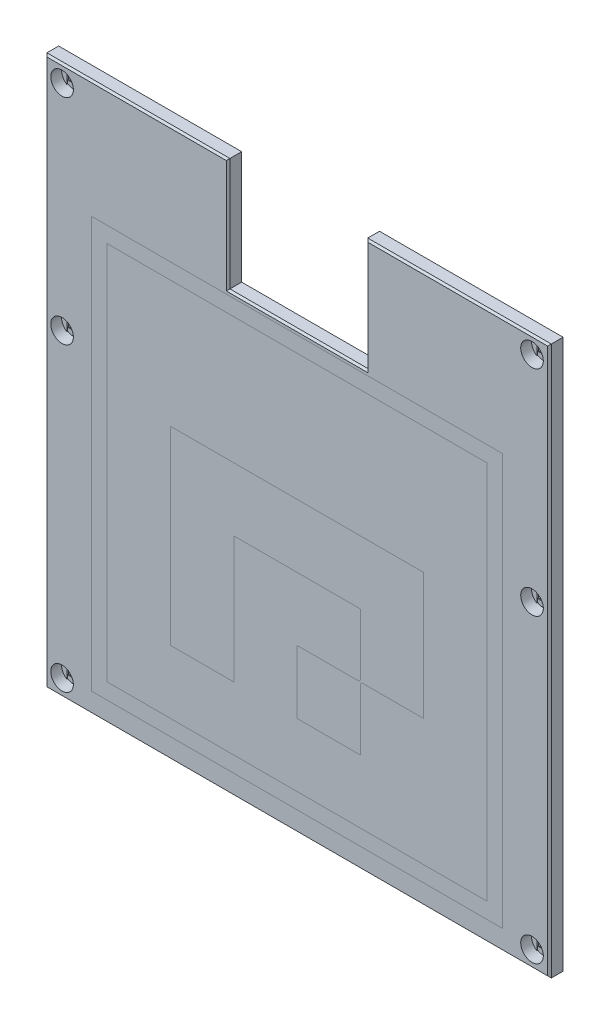
SolidWorks part; units mm, degrees
ref_plane "Front Plane" through (0, 0, 0) normal (0, 0, 1) x (1, 0, 0)
ref_plane "Top Plane" through (0, 0, 0) normal (0, 1, 0) x (1, 0, 0)
ref_plane "Right Plane" through (0, 0, 0) normal (1, 0, 0) x (0, 0, -1)
sketch "Sketch1" plane through (0, 0, 0) normal (0, 0, 1) x (1, 0, 0)
  line L0 (48, -68) -> (-48, -68) construction
  line L1 (56, -32.5) -> (56, -60) construction
  line L2 (56, 46) -> (56, -24.5) construction
  line L3 (-56, -24.5) -> (-56, 46) construction
  line L5 (-15, 54.4) -> (-15, 29) construction
  line L6 (-15, 29) -> (15, 29) construction
  line L8 (48, 54) -> (15, 54) construction
  line L9 (48, -68) -> (-48, -68) construction
  line L10 (56, -32.5) -> (56, -60) construction
  line L11 (56, 46) -> (56, -24.5) construction
  line L12 (-56, -24.5) -> (-56, 46) construction
  line L14 (-15, 54.4) -> (-15, 29) construction
  line L15 (-15, 29) -> (15, 29) construction
  line L16 (15, 29) -> (15, 54) construction
  line L17 (48, 54) -> (15, 54) construction
  line L18 (-15.25, 53.75) -> (-15.25, 28.75)
  line L19 (-55.75, 53.75) -> (-15.25, 53.75)
  line L20 (-55.75, 53.75) -> (-55.75, -67.75)
  line L21 (-55.75, -67.75) -> (55.875, -67.75)
  line L22 (55.875, 53.75) -> (55.875, -67.75)
  line L23 (-15.25, 28.75) -> (15.25, 28.75)
  line L24 (15.25, 28.75) -> (15.25, 53.75)
  line L25 (15.25, 53.75) -> (55.875, 53.75)
  circle A0 centre (-52, -64) radius 2.1 construction
  circle A3 centre (52, 50) radius 2.1 construction
  circle A4 centre (-52, 50) radius 2.1 construction
  circle A5 centre (-52, -64) radius 2.1 construction
  circle A6 centre (-52, 2.6) radius 2.15 construction
  circle A7 centre (52, 2.6) radius 2.15 construction
  circle A8 centre (52, 50) radius 2.1 construction
  circle A9 centre (-52, 50) radius 2.1 construction
  circle A10 centre (-52, 50) radius 1.35
  circle A11 centre (-52, 2.6) radius 1.35
  circle A12 centre (-52, -64) radius 1.35
  circle A13 centre (52, 50) radius 1.35
  circle A14 centre (52, 2.6) radius 1.35
  circle A15 centre (52, -64) radius 1.35
  circle A16 centre (-52, 2.6) radius 2.15 construction
  circle A17 centre (52, 2.6) radius 2.15 construction
  dimension "D5" = 2.7
  dimension "D1" = 0.25
  dimension "D2" = 0.25
  dimension "D3" = 0.25
  dimension "D4" = 0.25
  dimension "D6" = 0.25
  dimension "D7" = 0.25
  dimension "D8" = 0.25
extrude "Boss-Extrude1" add sketch "Sketch1" along normal blind 3
sketch "Sketch2" plane through (0, 0, 3) normal (0, 0, 1) x (1, 0, 0)
  line L5 (15.25, 28.75) -> (-15.25, 28.75) construction
  line L8 (-45.5, -63.25) -> (45.5, -63.25)
  line L9 (-45.5, -63.25) -> (-45.5, 27.75)
  line L10 (-45.5, 27.75) -> (45.5, 27.75)
  line L11 (45.5, -63.25) -> (45.5, 27.75)
  line L31 (-42, 24.25) -> (-28, 24.25)
  line L32 (-42, 24.25) -> (-42, 10.25)
  line L33 (-42, 10.25) -> (-28, 10.25)
  line L34 (-28, 24.25) -> (-28, 10.25)
  line L35 (-28, 24.25) -> (-14, 24.25)
  line L36 (-28, 24.25) -> (-28, 10.25)
  line L37 (-28, 10.25) -> (-14, 10.25)
  line L38 (-14, 24.25) -> (-14, 10.25)
  line L39 (-14, 24.25) -> (0, 24.25)
  line L40 (-14, 24.25) -> (-14, 10.25)
  line L41 (-14, 10.25) -> (0, 10.25)
  line L42 (0, 24.25) -> (0, 10.25)
  line L43 (0, 24.25) -> (14, 24.25)
  line L44 (0, 24.25) -> (0, 10.25)
  line L45 (0, 10.25) -> (14, 10.25)
  line L46 (14, 24.25) -> (14, 10.25)
  line L47 (14, 24.25) -> (28, 24.25)
  line L48 (14, 24.25) -> (14, 10.25)
  line L49 (14, 10.25) -> (28, 10.25)
  line L50 (28, 24.25) -> (28, 10.25)
  line L51 (28, 24.25) -> (42, 24.25)
  line L52 (28, 24.25) -> (28, 10.25)
  line L53 (28, 10.25) -> (42, 10.25)
  line L54 (42, 24.25) -> (42, 10.25)
  line L55 (-42, 10.25) -> (-28, 10.25)
  line L56 (-42, 10.25) -> (-42, -3.75)
  line L57 (-42, -3.75) -> (-28, -3.75)
  line L58 (-28, 10.25) -> (-28, -3.75)
  line L59 (-28, -3.75) -> (-14, -3.75)
  line L60 (-28, -3.75) -> (-28, 10.25)
  line L61 (-28, 10.25) -> (-14, 10.25)
  line L62 (-14, -3.75) -> (-14, 10.25)
  line L63 (-14, -3.75) -> (0, -3.75)
  line L64 (-14, -3.75) -> (-14, 10.25)
  line L65 (-14, 10.25) -> (0, 10.25)
  line L66 (0, -3.75) -> (0, 10.25)
  line L67 (0, -3.75) -> (14, -3.75)
  line L68 (0, -3.75) -> (0, 10.25)
  line L69 (0, 10.25) -> (14, 10.25)
  line L70 (14, -3.75) -> (14, 10.25)
  line L71 (14, -3.75) -> (28, -3.75)
  line L72 (14, -3.75) -> (14, 10.25)
  line L73 (14, 10.25) -> (28, 10.25)
  line L74 (28, -3.75) -> (28, 10.25)
  line L75 (28, -3.75) -> (42, -3.75)
  line L76 (28, -3.75) -> (28, 10.25)
  line L77 (28, 10.25) -> (42, 10.25)
  line L78 (42, -3.75) -> (42, 10.25)
  line L79 (42, -3.75) -> (28, -3.75)
  line L80 (42, -3.75) -> (42, -17.75)
  line L81 (42, -17.75) -> (28, -17.75)
  line L82 (28, -3.75) -> (28, -17.75)
  line L83 (14, -3.75) -> (28, -3.75)
  line L84 (14, -3.75) -> (14, -17.75)
  line L85 (14, -17.75) -> (28, -17.75)
  line L86 (28, -3.75) -> (28, -17.75)
  line L87 (0, -3.75) -> (14, -3.75)
  line L88 (0, -3.75) -> (0, -17.75)
  line L89 (0, -17.75) -> (14, -17.75)
  line L90 (14, -3.75) -> (14, -17.75)
  line L91 (-14, -3.75) -> (0, -3.75)
  line L92 (-14, -3.75) -> (-14, -17.75)
  line L93 (-14, -17.75) -> (0, -17.75)
  line L94 (0, -3.75) -> (0, -17.75)
  line L95 (-28, -3.75) -> (-14, -3.75)
  line L96 (-28, -3.75) -> (-28, -17.75)
  line L97 (-28, -17.75) -> (-14, -17.75)
  line L98 (-14, -3.75) -> (-14, -17.75)
  line L99 (-42, -3.75) -> (-28, -3.75)
  line L100 (-42, -3.75) -> (-42, -17.75)
  line L101 (-42, -17.75) -> (-28, -17.75)
  line L102 (-28, -3.75) -> (-28, -17.75)
  line L103 (-42, -17.75) -> (-28, -17.75)
  line L104 (-42, -17.75) -> (-42, -31.75)
  line L105 (-42, -31.75) -> (-28, -31.75)
  line L106 (-28, -17.75) -> (-28, -31.75)
  line L107 (-28, -31.75) -> (-14, -31.75)
  line L108 (-28, -31.75) -> (-28, -17.75)
  line L109 (-28, -17.75) -> (-14, -17.75)
  line L110 (-14, -31.75) -> (-14, -17.75)
  line L111 (-14, -17.75) -> (0, -17.75)
  line L112 (-14, -17.75) -> (-14, -31.75)
  line L113 (-14, -31.75) -> (0, -31.75)
  line L114 (0, -17.75) -> (0, -31.75)
  line L115 (0, -31.75) -> (14, -31.75)
  line L116 (0, -31.75) -> (0, -17.75)
  line L117 (0, -17.75) -> (14, -17.75)
  line L118 (14, -31.75) -> (14, -17.75)
  line L119 (14, -31.75) -> (28, -31.75)
  line L120 (14, -31.75) -> (14, -17.75)
  line L121 (14, -17.75) -> (28, -17.75)
  line L122 (28, -31.75) -> (28, -17.75)
  line L123 (28, -31.75) -> (42, -31.75)
  line L124 (28, -31.75) -> (28, -17.75)
  line L125 (28, -17.75) -> (42, -17.75)
  line L126 (42, -31.75) -> (42, -17.75)
  line L127 (-42, -31.75) -> (-28, -31.75)
  line L128 (-42, -31.75) -> (-42, -45.75)
  line L129 (-42, -45.75) -> (-28, -45.75)
  line L130 (-28, -31.75) -> (-28, -45.75)
  line L131 (-28, -45.75) -> (-14, -45.75)
  line L132 (-28, -45.75) -> (-28, -31.75)
  line L133 (-28, -31.75) -> (-14, -31.75)
  line L134 (-14, -45.75) -> (-14, -31.75)
  line L135 (-14, -45.75) -> (0, -45.75)
  line L136 (-14, -45.75) -> (-14, -31.75)
  line L137 (-14, -31.75) -> (0, -31.75)
  line L138 (0, -45.75) -> (0, -31.75)
  line L139 (0, -45.75) -> (14, -45.75)
  line L140 (0, -45.75) -> (0, -31.75)
  line L141 (0, -31.75) -> (14, -31.75)
  line L142 (14, -45.75) -> (14, -31.75)
  line L143 (14, -45.75) -> (28, -45.75)
  line L144 (14, -45.75) -> (14, -31.75)
  line L145 (14, -31.75) -> (28, -31.75)
  line L146 (28, -45.75) -> (28, -31.75)
  line L147 (28, -45.75) -> (42, -45.75)
  line L148 (28, -45.75) -> (28, -31.75)
  line L149 (28, -31.75) -> (42, -31.75)
  line L150 (42, -45.75) -> (42, -31.75)
  line L151 (42, -45.75) -> (28, -45.75)
  line L152 (42, -45.75) -> (42, -59.75)
  line L153 (42, -59.75) -> (28, -59.75)
  line L154 (28, -45.75) -> (28, -59.75)
  line L155 (28, -59.75) -> (14, -59.75)
  line L156 (28, -59.75) -> (28, -45.75)
  line L157 (28, -45.75) -> (14, -45.75)
  line L158 (14, -59.75) -> (14, -45.75)
  line L159 (0, -45.75) -> (14, -45.75)
  line L160 (0, -45.75) -> (0, -59.75)
  line L161 (0, -59.75) -> (14, -59.75)
  line L162 (14, -45.75) -> (14, -59.75)
  line L163 (-14, -45.75) -> (0, -45.75)
  line L164 (-14, -45.75) -> (-14, -59.75)
  line L165 (-14, -59.75) -> (0, -59.75)
  line L166 (0, -45.75) -> (0, -59.75)
  line L167 (-28, -45.75) -> (-14, -45.75)
  line L168 (-28, -45.75) -> (-28, -59.75)
  line L169 (-28, -59.75) -> (-14, -59.75)
  line L170 (-14, -45.75) -> (-14, -59.75)
  line L171 (-42, -45.75) -> (-28, -45.75)
  line L172 (-42, -45.75) -> (-42, -59.75)
  line L173 (-42, -59.75) -> (-28, -59.75)
  line L174 (-28, -45.75) -> (-28, -59.75)
  point P3 (0, 27.75)
  point P58 (-45.5, -17.75)
  dimension "D1" = 1
  dimension "D2" = 91
  dimension "D3" = 14
sketch "Sketch3" plane through (0, 0, 3) normal (0, 0, 1) x (1, 0, 0)
  circle A0 centre (-52, 50) radius 2.5
  circle A1 centre (-52, 2.6) radius 2.5
  circle A2 centre (-52, -64) radius 2.5
  circle A3 centre (52, -64) radius 2.5
  circle A4 centre (52, 2.6) radius 2.5
  circle A5 centre (52, 50) radius 2.5
  dimension "D1" = 5
extrude "Cut-Extrude1" cut sketch "Sketch3" against normal blind 2.4
sketch "Sketch4" plane through (0, 0, 0) normal (0, 0, -1) x (-1, 0, 0)
  line L0 (-15.25, 28.75) -> (15.25, 28.75) construction
  line L1 (-45.75, -57.75) -> (45.75, -57.75)
  line L2 (-45.75, -57.75) -> (-45.75, 27.75)
  line L3 (-45.75, 27.75) -> (45.75, 27.75)
  line L4 (45.75, -57.75) -> (45.75, 27.75)
  line L5 (-45.75, -57.75) -> (45.75, 27.75) construction
  line L6 (-45.75, 27.75) -> (45.75, -57.75) construction
  line L7 (55.75, 53.75) -> (55.75, -67.75) construction
  line L8 (55.75, -67.75) -> (-55.875, -67.75) construction
  point P0 (0, -15)
  point P9 (0, 27.75)
  dimension "D1" = 1
  dimension "D2" = 10
  dimension "D3" = 10
extrude "Cut-Extrude2" cut sketch "Sketch4" against normal blind 1.5
sketch "Sketch5" plane through (0, 0, 0.6) normal (0, 0, 1) x (1, 0, 0)
  line L2 (-53.35, 47.8958) -> (-53.35, 52.1042)
  line L4 (-50.65, 47.8958) -> (-50.65, 52.1042)
  line L5 (-53.35, 47.8958) -> (-50.65, 52.1042) construction
  line L6 (-53.35, 52.1042) -> (-50.65, 47.8958) construction
  line L8 (-53.35, 0.4958) -> (-53.35, 4.7042)
  line L10 (-50.65, 0.4958) -> (-50.65, 4.7042)
  line L11 (-53.35, 0.4958) -> (-50.65, 4.7042) construction
  line L12 (-53.35, 4.7042) -> (-50.65, 0.4958) construction
  line L14 (-53.35, -66.1042) -> (-53.35, -61.8958)
  line L16 (-50.65, -66.1042) -> (-50.65, -61.8958)
  line L17 (-53.35, -66.1042) -> (-50.65, -61.8958) construction
  line L18 (-53.35, -61.8958) -> (-50.65, -66.1042) construction
  circle A0 centre (-52, 50) radius 2.5 construction
  circle A1 centre (-52, 50) radius 1.35 construction
  arc A2 (-50.65, 52.1042) -> (-53.35, 52.1042) centre (-52, 50) ccw
  arc A3 (-53.35, 47.8958) -> (-50.65, 47.8958) centre (-52, 50) ccw
  circle A4 centre (-52, 2.6) radius 2.5 construction
  circle A5 centre (-52, 2.6) radius 1.35 construction
  circle A6 centre (-52, 2.6) radius 2.5 construction
  arc A7 (-50.65, 4.7042) -> (-53.35, 4.7042) centre (-52, 2.6) ccw
  arc A8 (-53.35, 0.4958) -> (-50.65, 0.4958) centre (-52, 2.6) ccw
  circle A9 centre (-52, -64) radius 2.5 construction
  circle A10 centre (-52, -64) radius 1.35 construction
  circle A11 centre (-52, -64) radius 2.5 construction
  arc A12 (-50.65, -61.8958) -> (-53.35, -61.8958) centre (-52, -64) ccw
  arc A13 (-53.35, -66.1042) -> (-50.65, -66.1042) centre (-52, -64) ccw
  point P0 (-52, 50)
  point P10 (-52, 2.6)
  point P22 (-52, -64)
extrude "Cut-Extrude3" cut sketch "Sketch5" against normal blind 0.2
sketch "Sketch6" plane through (0, 0, 0.4) normal (0, 0, 1) x (1, 0, 0)
  line L0 (-50.65, -66.1042) -> (-50.65, -61.8958) construction
  line L1 (-53.35, -65.35) -> (-50.65, -65.35)
  line L2 (-53.35, -65.35) -> (-53.35, -62.65)
  line L3 (-53.35, -62.65) -> (-50.65, -62.65)
  line L4 (-50.65, -65.35) -> (-50.65, -62.65)
  line L5 (-53.35, -65.35) -> (-50.65, -62.65) construction
  line L6 (-53.35, -62.65) -> (-50.65, -65.35) construction
  line L7 (-50.65, 0.4958) -> (-50.65, 4.7042) construction
  line L8 (-53.35, 1.25) -> (-50.65, 1.25)
  line L9 (-53.35, 1.25) -> (-53.35, 3.95)
  line L10 (-53.35, 3.95) -> (-50.65, 3.95)
  line L11 (-50.65, 1.25) -> (-50.65, 3.95)
  line L12 (-53.35, 1.25) -> (-50.65, 3.95) construction
  line L13 (-53.35, 3.95) -> (-50.65, 1.25) construction
  line L14 (-50.65, 47.8958) -> (-50.65, 52.1042) construction
  line L15 (-53.35, 48.65) -> (-50.65, 48.65)
  line L16 (-53.35, 48.65) -> (-53.35, 51.35)
  line L17 (-53.35, 51.35) -> (-50.65, 51.35)
  line L18 (-50.65, 48.65) -> (-50.65, 51.35)
  line L19 (-53.35, 48.65) -> (-50.65, 51.35) construction
  line L20 (-53.35, 51.35) -> (-50.65, 48.65) construction
  arc A0 (-50.65, -64) -> (-53.35, -64) centre (-52, -64) ccw construction
  arc A1 (-50.65, 2.6) -> (-53.35, 2.6) centre (-52, 2.6) ccw construction
  arc A2 (-50.65, 50) -> (-53.35, 50) centre (-52, 50) ccw construction
  point P0 (-52, -64)
  point P11 (-52, 2.6)
  point P22 (-52, 50)
extrude "Cut-Extrude4" cut sketch "Sketch6" against normal blind 0.2
mirror "Mirror1" about plane through (0, 0, 0) normal (1, 0, 0) of "Cut-Extrude4", "Cut-Extrude3"
chamfer "Chamfer1" distance 0.4 angle 45 3 edges at (0, 28.75, 3) (-15.25, 41.25, 3) (-35.5, 53.75, 3)
sketch "Sketch7" plane through (0, 0, 3) normal (0, 0, 1) x (1, 0, 0)
  line L0 (28, 24.25) -> (42, 24.25) construction
  line L1 (14, 24.25) -> (28, 24.25) construction
  line L2 (0, 24.25) -> (14, 24.25) construction
  line L3 (-14, 24.25) -> (0, 24.25) construction
  line L4 (-28, 24.25) -> (-14, 24.25) construction
  line L5 (-42, 24.25) -> (-28, 24.25) construction
  line L6 (-42, 24.25) -> (-42, 10.25) construction
  line L7 (-42, 10.25) -> (-42, -3.75) construction
  line L8 (-42, -3.75) -> (-42, -17.75) construction
  line L9 (-42, -17.75) -> (-42, -31.75) construction
  line L10 (-42, -31.75) -> (-42, -45.75) construction
  line L11 (-42, -45.75) -> (-42, -59.75) construction
  line L12 (-42, -59.75) -> (-28, -59.75) construction
  line L13 (-28, -59.75) -> (-14, -59.75) construction
  line L14 (-14, -59.75) -> (0, -59.75) construction
  line L15 (0, -59.75) -> (14, -59.75) construction
  line L16 (28, -59.75) -> (14, -59.75) construction
  line L17 (42, -59.75) -> (28, -59.75) construction
  line L18 (42, -45.75) -> (42, -59.75) construction
  line L19 (42, -45.75) -> (42, -31.75) construction
  line L20 (42, -31.75) -> (42, -17.75) construction
  line L21 (42, -3.75) -> (42, -17.75) construction
  line L22 (42, -3.75) -> (42, 10.25) construction
  line L23 (42, 24.25) -> (42, 10.25) construction
  line L24 (45.5, -63.25) -> (45.5, 27.75) construction
  line L25 (-45.5, -63.25) -> (45.5, -63.25) construction
  line L26 (-45.5, -63.25) -> (-45.5, 27.75) construction
  line L27 (-45.5, 27.75) -> (45.5, 27.75) construction
  line L28 (28, 24.25) -> (42, 24.25)
  line L29 (14, 24.25) -> (28, 24.25)
  line L30 (0, 24.25) -> (14, 24.25)
  line L31 (-14, 24.25) -> (0, 24.25)
  line L32 (-28, 24.25) -> (-14, 24.25)
  line L33 (-42, 24.25) -> (-28, 24.25)
  line L34 (-42, 24.25) -> (-42, 10.25)
  line L35 (-42, 10.25) -> (-42, -3.75)
  line L36 (-42, -3.75) -> (-42, -17.75)
  line L37 (-42, -17.75) -> (-42, -31.75)
  line L38 (-42, -31.75) -> (-42, -45.75)
  line L39 (-42, -45.75) -> (-42, -59.75)
  line L40 (-42, -59.75) -> (-28, -59.75)
  line L41 (-28, -59.75) -> (-14, -59.75)
  line L42 (-14, -59.75) -> (0, -59.75)
  line L43 (0, -59.75) -> (14, -59.75)
  line L44 (28, -59.75) -> (14, -59.75)
  line L45 (42, -59.75) -> (28, -59.75)
  line L46 (42, -45.75) -> (42, -59.75)
  line L47 (42, -45.75) -> (42, -31.75)
  line L48 (42, -31.75) -> (42, -17.75)
  line L49 (42, -3.75) -> (42, -17.75)
  line L50 (42, -3.75) -> (42, 10.25)
  line L51 (42, 24.25) -> (42, 10.25)
  line L52 (45.5, -63.25) -> (45.5, 27.75)
  line L53 (-45.5, -63.25) -> (45.5, -63.25)
  line L54 (-45.5, -63.25) -> (-45.5, 27.75)
  line L55 (-45.5, 27.75) -> (45.5, 27.75)
extrude "Cut-Extrude5" cut sketch "Sketch7" against normal blind 0.4
sketch "Sketch8" plane through (0, 0, 2.6) normal (0, 0, 1) x (1, 0, 0)
  line L0 (-42, -59.75) -> (42, -59.75) construction
  line L1 (42, -59.75) -> (42, 24.25) construction
  line L2 (42, 24.25) -> (-42, 24.25) construction
  line L3 (-42, 24.25) -> (-42, -59.75) construction
  line L4 (-45.5, -63.25) -> (45.5, -63.25)
  line L5 (45.5, -63.25) -> (45.5, 27.75)
  line L6 (45.5, 27.75) -> (-45.5, 27.75)
  line L7 (-45.5, 27.75) -> (-45.5, -63.25)
  line L8 (-45.5, -63.25) -> (45.5, -63.25)
  line L9 (45.5, -63.25) -> (45.5, 27.75)
  line L10 (45.5, 27.75) -> (-45.5, 27.75)
  line L11 (-45.5, 27.75) -> (-45.5, -63.25)
  line L12 (-42, -59.75) -> (42, -59.75)
  line L13 (42, -59.75) -> (42, 24.25)
  line L14 (42, 24.25) -> (-42, 24.25)
  line L15 (-42, 24.25) -> (-42, -59.75)
  dimension "D1" = 0
extrude "Boss-Extrude2" add sketch "Sketch8" along normal up to surface (0.4 mm away) separate body up to face at (0, -17.75, 3)
sketch "Sketch9" plane through (0, 0, 3) normal (0, 0, 1) x (1, 0, 0)
  line L0 (0, -45.75) -> (0, -31.75) construction
  line L1 (0, -45.75) -> (14, -45.75) construction
  line L2 (14, -45.75) -> (14, -31.75) construction
  line L3 (0, -31.75) -> (14, -31.75) construction
  line L4 (-14, -31.75) -> (-14, -17.75) construction
  line L5 (-14, -17.75) -> (0, -17.75) construction
  line L6 (0, -17.75) -> (14, -17.75) construction
  line L7 (14, -31.75) -> (14, -17.75) construction
  line L8 (14, -31.75) -> (28, -31.75) construction
  line L9 (28, -31.75) -> (28, -17.75) construction
  line L10 (28, -3.75) -> (28, -17.75) construction
  line L11 (14, -3.75) -> (28, -3.75) construction
  line L12 (0, -3.75) -> (14, -3.75) construction
  line L13 (-14, -3.75) -> (0, -3.75) construction
  line L14 (-28, -3.75) -> (-14, -3.75) construction
  line L15 (-28, -3.75) -> (-28, -17.75) construction
  line L16 (-28, -17.75) -> (-28, -31.75) construction
  line L17 (-28, -45.75) -> (-14, -45.75) construction
  line L18 (-14, -45.75) -> (-14, -31.75) construction
  line L19 (-28, -31.75) -> (-28, -45.75) construction
  line L20 (0, -45.75) -> (0, -31.75)
  line L21 (0, -45.75) -> (14, -45.75)
  line L22 (14, -45.75) -> (14, -32.1036)
  line L23 (0, -31.75) -> (13.6464, -31.75)
  line L24 (-14, -31.75) -> (-14, -17.75)
  line L25 (-14, -17.75) -> (0, -17.75)
  line L26 (0, -17.75) -> (14, -17.75)
  line L27 (14, -31.3964) -> (14, -17.75)
  line L28 (14.3536, -31.75) -> (28, -31.75)
  line L29 (28, -31.75) -> (28, -17.75)
  line L30 (28, -3.75) -> (28, -17.75)
  line L31 (14, -3.75) -> (28, -3.75)
  line L32 (0, -3.75) -> (14, -3.75)
  line L33 (-14, -3.75) -> (0, -3.75)
  line L34 (-28, -3.75) -> (-14, -3.75)
  line L35 (-28, -3.75) -> (-28, -17.75)
  line L36 (-28, -17.75) -> (-28, -31.75)
  line L37 (-28, -45.75) -> (-14, -45.75)
  line L38 (-14, -45.75) -> (-14, -31.75)
  line L39 (-28, -31.75) -> (-28, -45.75)
  line L40 (13.6464, -31.75) -> (14, -31.3964)
  line L41 (14.3536, -31.75) -> (14, -32.1036)
  dimension "D1" = 45
  dimension "D2" = 0.5
extrude "Cut-Extrude6" cut sketch "Sketch9" against normal blind 0.4 contours L23 L20 L21 L22 | L36 L39 L37 L38 L24 L25 L26 L27 L28 L29 L30 L31 L32 L33 L34 L35
sketch "Sketch10" plane through (0, 0, 2.6) normal (0, 0, 1) x (1, 0, 0)
  line L38 (14, -32.1036) -> (14.3536, -31.75)
  line L39 (14.3536, -31.75) -> (28, -31.75)
  line L40 (28, -31.75) -> (28, -3.75)
  line L41 (28, -3.75) -> (-28, -3.75)
  line L42 (-28, -3.75) -> (-28, -45.75)
  line L43 (-28, -45.75) -> (-14, -45.75)
  line L44 (-14, -45.75) -> (-14, -17.75)
  line L45 (-14, -17.75) -> (14, -17.75)
  line L46 (14, -17.75) -> (14, -31.3964)
  line L47 (14, -31.3964) -> (13.6464, -31.75)
  line L48 (13.6464, -31.75) -> (0, -31.75)
  line L49 (0, -31.75) -> (0, -45.75)
  line L50 (0, -45.75) -> (14, -45.75)
  line L51 (14, -45.75) -> (14, -32.1036)
  line L52 (14, -32.1036) -> (14.3536, -31.75)
  line L53 (14.3536, -31.75) -> (28, -31.75)
  line L54 (28, -31.75) -> (28, -3.75)
  line L55 (28, -3.75) -> (-28, -3.75)
  line L56 (-28, -3.75) -> (-28, -45.75)
  line L57 (-28, -45.75) -> (-14, -45.75)
  line L58 (-14, -45.75) -> (-14, -17.75)
  line L59 (-14, -17.75) -> (14, -17.75)
  line L60 (14, -17.75) -> (14, -31.3964)
  line L61 (14, -31.3964) -> (13.6464, -31.75)
  line L62 (13.6464, -31.75) -> (0, -31.75)
  line L63 (0, -31.75) -> (0, -45.75)
  line L64 (0, -45.75) -> (14, -45.75)
  line L65 (14, -45.75) -> (14, -32.1036)
  dimension "D1" = 0
extrude "Boss-Extrude3" add sketch "Sketch10" along normal up to surface (0.4 mm away) separate body up to face at (0, -17.75, 3)
